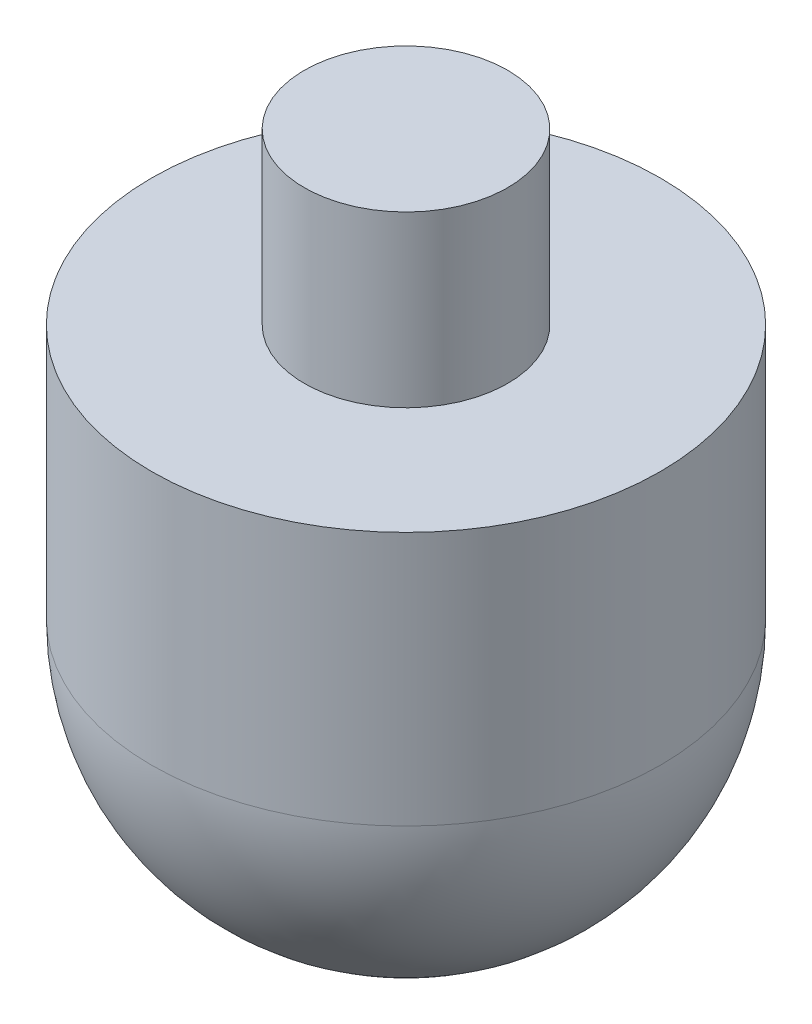
SolidWorks part; units mm, degrees
material "ABS"
ref_plane "Alzado" through (0, 0, 0) normal (0, 0, 1) x (1, 0, 0)
ref_plane "Planta" through (0, 0, 0) normal (0, 1, 0) x (1, 0, 0)
ref_plane "Vista lateral" through (0, 0, 0) normal (1, 0, 0) x (0, 0, -1)
sketch "Croquis1" plane through (0, 0, 0) normal (0, 0, 1) x (1, 0, 0)
  line L0 (0, 0) -> (0, 43.7045) construction
  line L1 (0, 40) -> (6, 40)
  line L2 (6, 40) -> (6, 30)
  line L3 (6, 30) -> (15, 30)
  line L4 (15, 30) -> (15, 15)
  line L5 (0, 0) -> (0, 40)
  arc A0 (15, 15) -> (0, 0) centre (0, 15) cw
  dimension "D1" = 12
  dimension "D2" = 30
  dimension "D3" = 10
  dimension "D4" = 25
revolve "Revolución1" add sketch "Croquis1" angle 360 about L0
